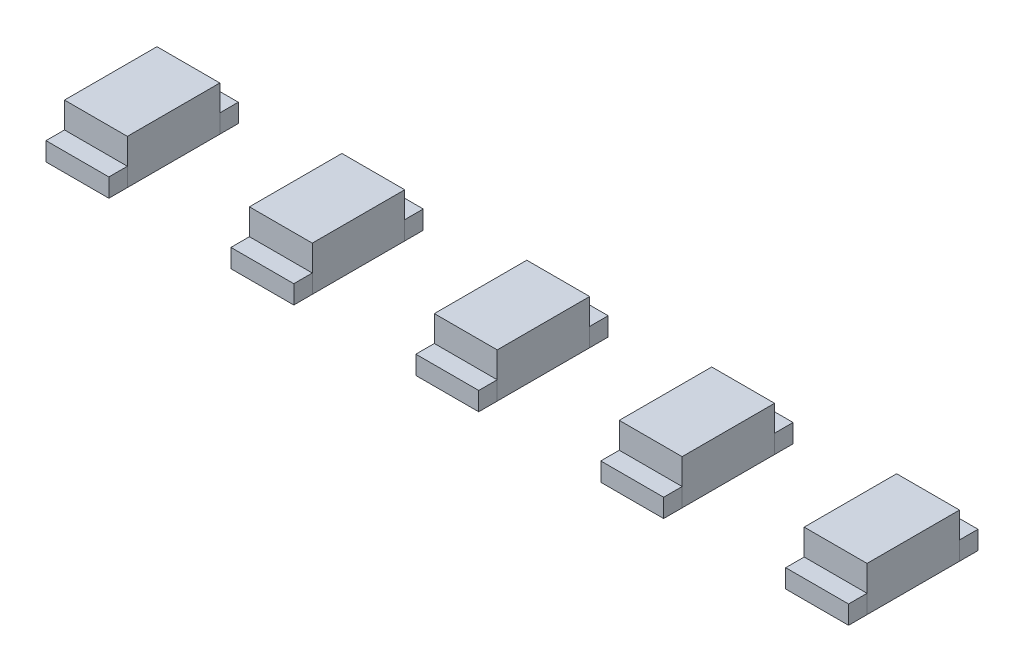
SolidWorks part; units mm, degrees
ref_plane "Front" through (0, 0, 0) normal (0, 0, 1) x (1, 0, 0)
ref_plane "Top" through (0, 0, 0) normal (0, 1, 0) x (1, 0, 0)
ref_plane "Right" through (0, 0, 0) normal (1, 0, 0) x (0, 0, -1)
sketch "Sketch1" plane through (0, 0, 0) normal (0, 1, 0) x (1, 0, 0)
  line L0 (0, 3.5488) -> (0, 0) construction
  line L1 (-5.425, 0.625) -> (-4.575, 0.625)
  line L2 (-5.425, 0.625) -> (-5.425, -0.625)
  line L3 (-5.425, -0.625) -> (-4.575, -0.625)
  line L4 (-4.575, 0.625) -> (-4.575, -0.625)
  line L5 (0, 0) -> (3.4283, 0) construction
  line L6 (4.575, 0.625) -> (4.575, -0.625)
  line L7 (5.425, -0.625) -> (4.575, -0.625)
  line L8 (5.425, 0.625) -> (5.425, -0.625)
  line L9 (5.425, 0.625) -> (4.575, 0.625)
  line L10 (-2.925, 0.625) -> (-2.075, 0.625)
  line L11 (-2.925, 0.625) -> (-2.925, -0.625)
  line L12 (-2.925, -0.625) -> (-2.075, -0.625)
  line L13 (-2.075, 0.625) -> (-2.075, -0.625)
  line L14 (-0.425, 0.625) -> (0.425, 0.625)
  line L15 (-0.425, 0.625) -> (-0.425, -0.625)
  line L16 (-0.425, -0.625) -> (0.425, -0.625)
  line L17 (0.425, 0.625) -> (0.425, -0.625)
  line L18 (2.075, 0.625) -> (2.075, -0.625)
  line L19 (2.925, -0.625) -> (2.075, -0.625)
  line L20 (2.925, 0.625) -> (2.925, -0.625)
  line L21 (2.925, 0.625) -> (2.075, 0.625)
  line L22 (-4.575, 0.625) -> (-2.925, 0.625) construction
  line L23 (-2.075, 0.625) -> (-0.425, 0.625) construction
  line L24 (0.425, 0.625) -> (2.075, 0.625) construction
  line L25 (2.925, 0.625) -> (4.575, 0.625) construction
  point P8 (-4.575, 0)
  point P22 (0.425, 0)
  point P23 (0, 0.625)
  dimension "D1" = 1.25
  dimension "D2" = 0.85
  dimension "D3" = 10.85
extrude "Boss-Extrude1" add sketch "Sketch1" along normal blind 0.6
sketch "Sketch2" plane through (0, 0, 0) normal (0, 1, 0) x (1, 0, 0)
  line L0 (-2.925, 0.625) -> (-2.925, -0.625) construction
  line L1 (-5.425, 0.875) -> (-4.575, 0.875)
  line L2 (-5.425, 0.875) -> (-5.425, 0.625)
  line L3 (-5.425, 0.625) -> (-4.575, 0.625)
  line L4 (-4.575, 0.875) -> (-4.575, 0.625)
  line L5 (-2.925, 0.875) -> (-2.075, 0.875)
  line L6 (-2.925, 0.875) -> (-2.925, 0.625)
  line L7 (-2.925, 0.625) -> (-2.075, 0.625)
  line L8 (-2.075, 0.875) -> (-2.075, 0.625)
  line L9 (-0.425, 0.875) -> (0.425, 0.875)
  line L10 (-0.425, 0.875) -> (-0.425, 0.625)
  line L11 (-0.425, 0.625) -> (0.425, 0.625)
  line L12 (0.425, 0.875) -> (0.425, 0.625)
  line L13 (-5.425, 0.625) -> (-5.425, -0.625) construction
  line L14 (-0.425, 0.625) -> (-0.425, -0.625) construction
  line L15 (0, 3.4735) -> (0, 0) construction
  line L16 (0, 3.5488) -> (0, 0) construction
  line L17 (0, 0) -> (3.3183, 0) construction
  line L18 (0, 0) -> (3.4283, 0) construction
  line L19 (2.075, 0.875) -> (2.075, 0.625)
  line L20 (2.925, 0.625) -> (2.075, 0.625)
  line L21 (2.925, 0.875) -> (2.925, 0.625)
  line L22 (2.925, 0.875) -> (2.075, 0.875)
  line L23 (4.575, 0.875) -> (4.575, 0.625)
  line L24 (5.425, 0.625) -> (4.575, 0.625)
  line L25 (5.425, 0.875) -> (5.425, 0.625)
  line L26 (5.425, 0.875) -> (4.575, 0.875)
  line L27 (5.425, -0.875) -> (4.575, -0.875)
  line L28 (5.425, -0.875) -> (5.425, -0.625)
  line L29 (5.425, -0.625) -> (4.575, -0.625)
  line L30 (4.575, -0.875) -> (4.575, -0.625)
  line L31 (2.925, -0.875) -> (2.075, -0.875)
  line L32 (2.925, -0.875) -> (2.925, -0.625)
  line L33 (2.925, -0.625) -> (2.075, -0.625)
  line L34 (2.075, -0.875) -> (2.075, -0.625)
  line L35 (0.425, -0.875) -> (0.425, -0.625)
  line L36 (-0.425, -0.625) -> (0.425, -0.625)
  line L37 (-0.425, -0.875) -> (-0.425, -0.625)
  line L38 (-0.425, -0.875) -> (0.425, -0.875)
  line L39 (-2.075, -0.875) -> (-2.075, -0.625)
  line L40 (-2.925, -0.625) -> (-2.075, -0.625)
  line L41 (-2.925, -0.875) -> (-2.925, -0.625)
  line L42 (-2.925, -0.875) -> (-2.075, -0.875)
  line L43 (-4.575, -0.875) -> (-4.575, -0.625)
  line L44 (-5.425, -0.625) -> (-4.575, -0.625)
  line L45 (-5.425, -0.875) -> (-5.425, -0.625)
  line L46 (-5.425, -0.875) -> (-4.575, -0.875)
  dimension "D1" = 0.25
extrude "Boss-Extrude2" add sketch "Sketch2" along normal blind 0.25
sketch "Sketch3" plane through (-5.425, 0, 0) normal (-1, 0, 0) x (0, 0, 1)
  line L0 (0.625, 0.25) -> (0.625, 0)
  line L1 (-0.875, 0) -> (0.875, 0) construction
  line L2 (-0.625, 0.25) -> (-0.625, 0)
split line "Split Line1"
